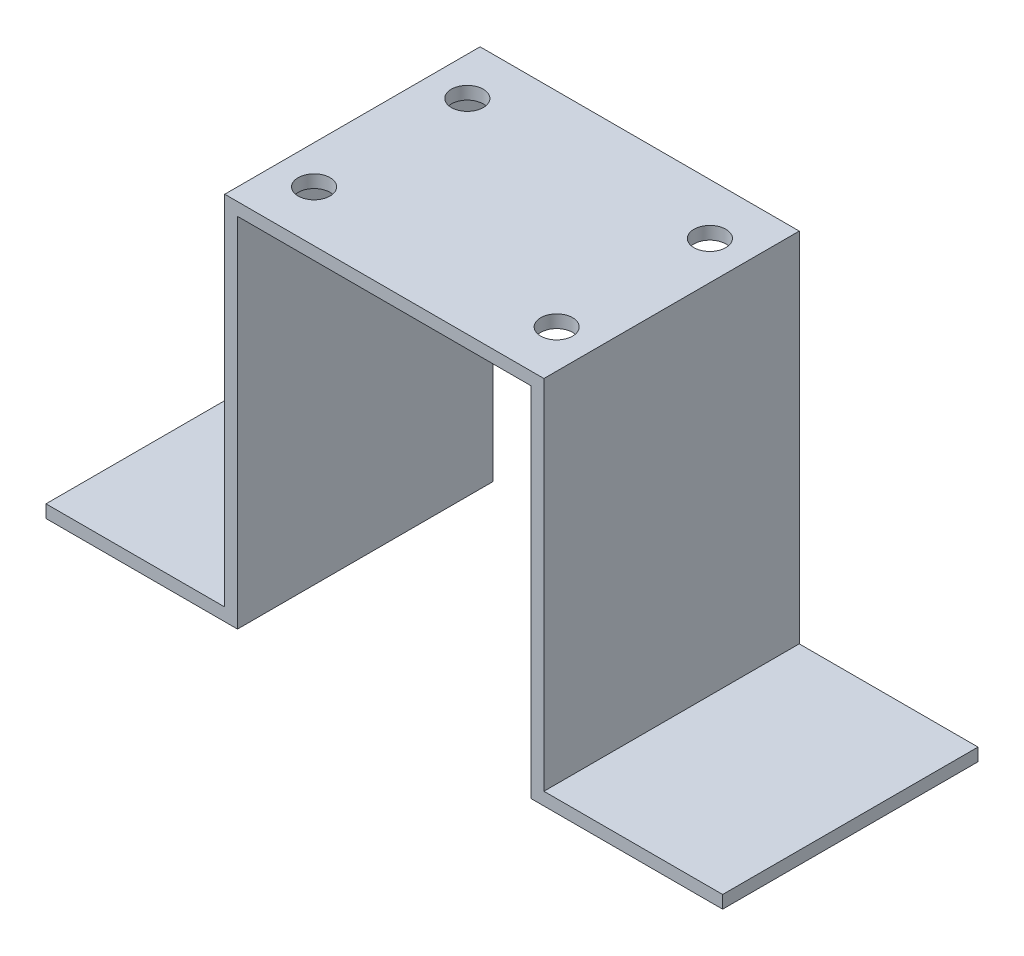
SolidWorks part; units mm, degrees
material "Plain Carbon Steel"
ref_plane "Front Plane" through (0, 0, 0) normal (0, 0, 1) x (1, 0, 0)
ref_plane "Top Plane" through (0, 0, 0) normal (0, 1, 0) x (1, 0, 0)
ref_plane "Right Plane" through (0, 0, 0) normal (1, 0, 0) x (0, 0, -1)
sketch "Sketch11" plane through (0, 0, 0) normal (0, 0, 1) x (1, 0, 0)
  line L0 (0, 0) -> (38.1, 0)
  line L1 (38.1, 0) -> (38.1, 71.12)
  line L2 (38.1, 71.12) -> (96.52, 71.12)
  line L3 (38.1, 71.12) -> (38.1, 73.66) construction
  line L4 (96.52, 71.12) -> (96.52, 0)
  line L5 (96.52, 0) -> (134.62, 0)
  line L6 (134.62, 0) -> (134.62, 2.54)
  line L7 (134.62, 2.54) -> (99.06, 2.54)
  line L8 (99.06, 2.54) -> (99.06, 73.66)
  line L10 (99.06, 73.66) -> (35.56, 73.66)
  line L11 (35.56, 73.66) -> (35.56, 2.54)
  line L12 (35.56, 2.54) -> (0, 2.54)
  line L13 (0, 2.54) -> (0, 0)
  line L16 (35.56, 2.54) -> (38.1, 2.54) construction
  line L17 (99.06, 2.54) -> (96.52, 2.54) construction
  dimension "D1" = 38.1
  dimension "D2" = 2.54
  dimension "D3" = 2.54
  dimension "D4" = 71.12
  dimension "D5" = 63.5
extrude "Boss-Extrude1" add sketch "Sketch11" against normal blind 50.8
sketch "Sketch12" plane through (0, 73.66, 0) normal (0, 1, 0) x (1, 0, 0)
  line L0 (43.18, 0) -> (43.18, 10.16) construction
  line L1 (99.06, 0) -> (35.56, 0) construction
  line L2 (43.18, 10.16) -> (35.56, 10.16) construction
  line L3 (35.56, 50.8) -> (35.56, 0) construction
  line L4 (99.06, 10.16) -> (91.44, 10.16) construction
  line L5 (99.06, 50.8) -> (99.06, 0) construction
  line L6 (91.44, 10.16) -> (91.44, 0) construction
  line L7 (91.44, 50.8) -> (91.44, 40.64) construction
  line L8 (99.06, 50.8) -> (35.56, 50.8) construction
  line L9 (91.44, 40.64) -> (99.06, 40.64) construction
  line L10 (43.18, 50.8) -> (43.18, 40.64) construction
  line L11 (43.18, 40.64) -> (35.56, 40.64) construction
  circle A0 centre (43.18, 10.16) radius 3.175
  circle A1 centre (91.44, 10.16) radius 3.175
  circle A2 centre (91.44, 40.64) radius 3.175
  circle A3 centre (43.18, 40.64) radius 3.175
  dimension "D1" = 7.62
  dimension "D2" = 10.16
extrude "Cut-Extrude1" cut sketch "Sketch12" against normal up to next
